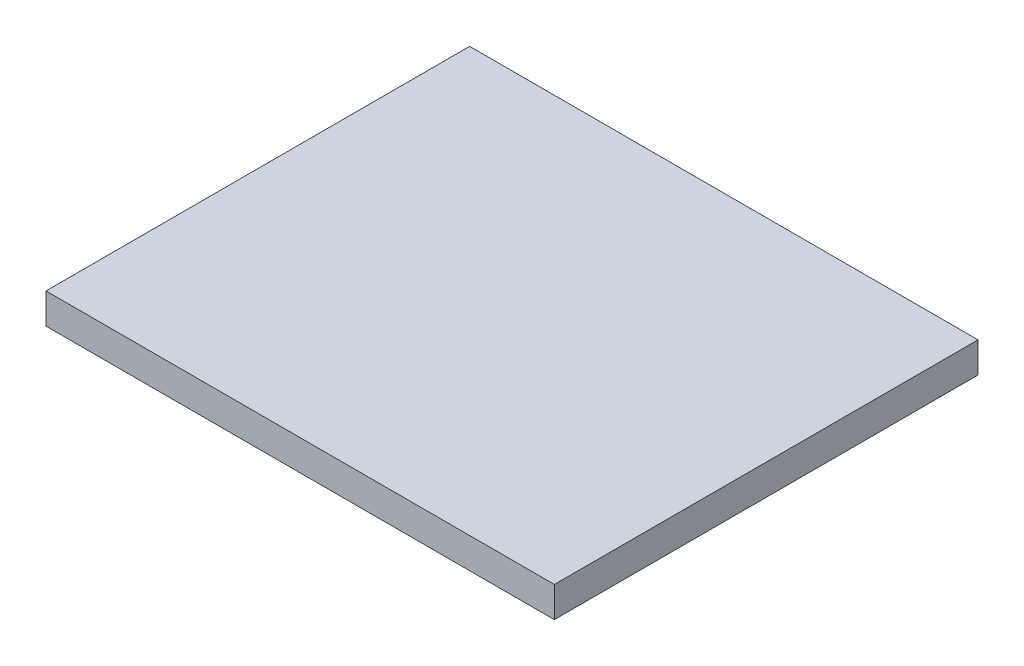
SolidWorks part; units mm, degrees
material "Pin"
ref_plane "Plan de face" through (0, 0, 0) normal (0, 0, 1) x (1, 0, 0)
ref_plane "Plan de dessus" through (0, 0, 0) normal (0, 1, 0) x (1, 0, 0)
ref_plane "Plan de droite" through (0, 0, 0) normal (1, 0, 0) x (0, 0, -1)
sketch "Esquisse1" plane through (0, 0, 0) normal (0, 1, 0) x (1, 0, 0)
  line L0 (-37.8396, -18.0564) -> (-37.8396, 1.9436) construction
  line L1 (-68.0491, 47.6831) -> (231.9509, 47.6831)
  line L2 (-68.0491, 47.6831) -> (-68.0491, -202.3169)
  line L3 (-68.0491, -202.3169) -> (231.9509, -202.3169)
  line L4 (231.9509, 47.6831) -> (231.9509, -202.3169)
  line L5 (-37.8396, -18.0564) -> (-37.8396, -73.0564) construction
  line L6 (-37.8396, 1.9436) -> (-37.8396, 47.6831) construction
  line L7 (-37.8396, -73.0564) -> (-37.8396, -93.0564) construction
  line L8 (-37.8396, -93.0564) -> (-37.8396, -202.3169) construction
  dimension "D1" = 300
  dimension "D2" = 250
  dimension "D4" = 20
  dimension "D5" = 95
extrude "Boss.-Extru.1" add sketch "Esquisse1" along normal blind 18
